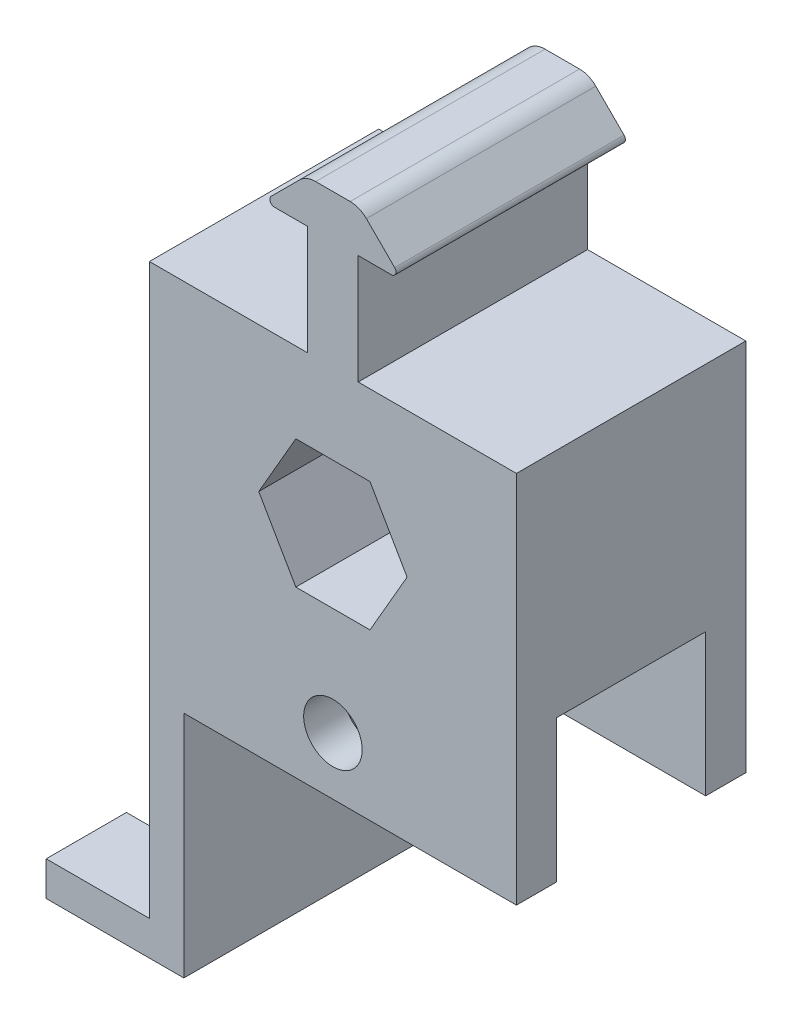
SolidWorks part; units mm, degrees
ref_plane "Front Plane" through (0, 0, 0) normal (0, 0, 1) x (1, 0, 0)
ref_plane "Top Plane" through (0, 0, 0) normal (0, 1, 0) x (1, 0, 0)
ref_plane "Right Plane" through (0, 0, 0) normal (1, 0, 0) x (0, 0, -1)
sketch "Sketch1" plane through (0, 0, 0) normal (0, 0, 1) x (1, 0, 0)
  line L0 (-20.32, 16.002) -> (-20.32, -25.4)
  line L1 (-4.1061, 7.112) -> (-8.2122, 0)
  line L2 (-8.2122, 0) -> (-4.1061, -7.112)
  line L3 (-4.1061, -7.112) -> (4.1061, -7.112)
  line L4 (4.1061, -7.112) -> (8.2122, 0)
  line L5 (8.2122, 0) -> (4.1061, 7.112)
  line L6 (4.1061, 7.112) -> (-4.1061, 7.112)
  line L7 (-20.32, -25.4) -> (20.32, -25.4)
  line L8 (20.32, -25.4) -> (20.32, 16.002)
  line L9 (-20.32, 16.002) -> (-2.794, 16.002)
  line L10 (-2.794, 16.002) -> (-2.794, 28.1305)
  line L11 (-2.794, 28.1305) -> (-6.477, 28.1305)
  line L12 (-6.8362, 28.9977) -> (-3.7065, 32.1275)
  line L13 (-1.9104, 32.8714) -> (1.9104, 32.8714)
  line L14 (0, 41.8096) -> (0, -25.778) construction
  line L15 (20.32, 16.002) -> (2.794, 16.002)
  line L16 (2.794, 16.002) -> (2.794, 28.1305)
  line L17 (6.8362, 28.9977) -> (3.7065, 32.1275)
  line L18 (2.794, 28.1305) -> (6.477, 28.1305)
  line L19 (-6.985, 28.6385) -> (6.985, 28.6385) construction
  circle A0 centre (0, 0) radius 7.112 construction
  arc A1 (-6.477, 28.1305) -> (-6.8362, 28.9977) centre (-6.477, 28.6385) cw
  arc A2 (-3.7065, 32.1275) -> (-1.9104, 32.8714) centre (-1.9104, 30.3314) cw
  arc A3 (3.7065, 32.1275) -> (1.9104, 32.8714) centre (1.9104, 30.3314) ccw
  arc A4 (6.477, 28.1305) -> (6.8362, 28.9977) centre (6.477, 28.6385) ccw
  point P18 (7.7034, 28.1305)
  point P21 (-4.6355, 28.1305)
  point P25 (-7.7034, 28.1305)
  point P29 (0, -25.4)
  point P35 (0, 32.8714)
  dimension "D7" = 0.508
  dimension "D8" = 2.54
  dimension "D1" = 14.224
  dimension "D2" = 21.0185
  dimension "D3" = 5.588
  dimension "D4" = 4.7409
  dimension "D5" = 135
  dimension "D6" = 13.97
  dimension "D9" = 25.4
  dimension "D10" = 8.89
  dimension "D11" = 20.32
extrude "Boss-Extrude1" add sketch "Sketch1" along normal mid plane 25.4
sketch "Sketch10" plane through (0, 0, 0) normal (0, 0, 1) x (1, 0, 0)
  line L0 (-20.32, -25.4) -> (-20.32, -46.99)
  line L1 (-20.32, -46.99) -> (-31.75, -46.99)
  line L2 (-31.75, -46.99) -> (-31.75, -50.8)
  line L3 (-31.75, -50.8) -> (-16.51, -50.8)
  line L4 (-16.51, -50.8) -> (-16.51, -25.4)
  line L5 (-20.32, -25.4) -> (20.32, -25.4) construction
  line L6 (-20.32, -25.4) -> (-16.51, -25.4)
  dimension "D2" = 21.59
  dimension "D3" = 3.81
  dimension "D4" = 11.43
extrude "Boss-Extrude4" add sketch "Sketch10" along normal up to surface and the other way up to surface up to face at (0, 19.615, 12.7) other way up to face at (0, 19.615, -12.7)
sketch "Sketch6" plane through (20.32, 0, 0) normal (1, 0, 0) x (0, 0, -1)
  line L0 (-12.7, -7.112) -> (12.7, -7.112) construction
  line L1 (-12.7, -7.112) -> (12.7, -7.112) construction
  line L2 (-8.255, -25.4) -> (-8.255, -9.652)
  line L3 (-8.255, -9.652) -> (8.255, -9.652)
  line L11 (-8.255, -25.4) -> (8.255, -25.4)
  line L12 (8.255, -9.652) -> (8.255, -25.4)
  point P10 (0, -9.652)
  dimension "D2" = 16.51
  dimension "D3" = 2.54
  dimension "D1" = 15.748
extrude "Cut-Extrude2" cut sketch "Sketch6" against normal through all
sketch "Sketch11" plane through (0, -46.99, 0) normal (0, 1, 0) x (1, 0, 0)
  line L0 (-31.75, -12.7) -> (-31.75, 12.7) construction
  line L1 (-20.32, -12.7) -> (-20.32, 12.7) construction
  line L2 (-31.75, -3.81) -> (-31.75, 3.81)
  line L3 (-20.32, -3.81) -> (-20.32, 3.81)
  line L4 (-31.75, 3.81) -> (-20.32, 3.81)
  line L5 (-31.75, -3.81) -> (-20.32, -3.81)
  point P8 (-20.32, 0)
  point P9 (-31.75, 0)
  dimension "D1" = 7.62
extrude "Cut-Extrude3" cut sketch "Sketch11" against normal up to surface (3.81 mm away) up to face at (-24.13, -50.8, 0)
sketch "Sketch15" plane through (0, 0, 12.7) normal (0, 0, 1) x (1, 0, 0)
  line L1 (-4.1061, -7.112) -> (4.1061, -7.112) construction
  circle A0 centre (0, -19.05) radius 3.2385
  point P7 (0, -7.112)
  dimension "D1" = 6.477
  dimension "D2" = 11.938
extrude "Cut-Extrude4" cut sketch "Sketch15" against normal up to surface (25.4 mm away) up to face at (-4.826, 5.913, -12.7)
